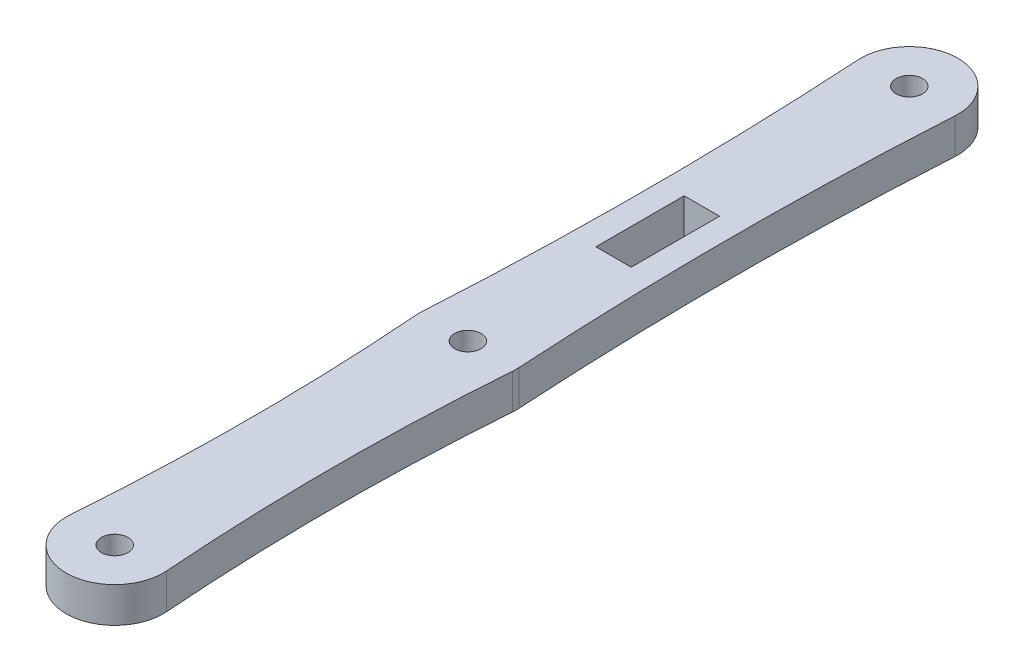
SolidWorks part; units mm, degrees
ref_plane "Front Plane" through (0, 0, 0) normal (0, 0, 1) x (1, 0, 0)
ref_plane "Top Plane" through (0, 0, 0) normal (0, 1, 0) x (1, 0, 0)
ref_plane "Right Plane" through (0, 0, 0) normal (1, 0, 0) x (0, 0, -1)
sketch "Sketch1" plane through (0, 0, 0) normal (0, 1, 0) x (1, 0, 0)
  line L0 (0, 0) -> (0, 90) construction
  line L3 (4.75, 65) -> (-4.75, 65) construction
  line L4 (4.75, 20) -> (-4.75, 20) construction
  line L6 (2, 56.5) -> (-2, 56.5)
  line L7 (2, 56.5) -> (2, 66.5)
  line L8 (2, 66.5) -> (-2, 66.5)
  line L9 (-2, 56.5) -> (-2, 66.5)
  circle A2 centre (0, 0) radius 1.5
  circle A3 centre (0, 90) radius 1.5
  arc A8 (-5.4846, 0.4119) -> (5.4846, 0.4119) centre (0, 0) ccw
  arc A9 (5.4901, 89.6703) -> (-5.4901, 89.6703) centre (0, 90) ccw
  circle A12 centre (0, 40) radius 1.5
  arc A13 (-5.4901, 40.3297) -> (-5.4846, 39.5881) centre (0, 40) ccw
  arc A14 (5.4846, 0.4119) -> (5.4846, 39.5881) centre (266.2917, 20) cw
  arc A15 (5.4901, 40.3297) -> (5.4901, 89.6703) centre (416.2917, 65) cw
  arc A16 (-5.4846, 0.4119) -> (-5.4846, 39.5881) centre (-266.2917, 20) ccw
  arc A17 (-5.4901, 40.3297) -> (-5.4901, 89.6703) centre (-416.2917, 65) ccw
  arc A18 (5.4846, 39.5881) -> (5.4901, 40.3297) centre (0, 40) ccw
  circle A19 centre (0, 65) radius 1.5 construction
  point P26 (0, 20)
  point P27 (0, 65)
  point P33 (-1.3122, 61.7212)
  point P34 (0, 66.5)
  dimension "D1" = 3
  dimension "D2" = 90
  dimension "D3" = 4
  dimension "D5" = 9.5
  dimension "D6" = 3
  dimension "D7" = 4
  dimension "D4" = 40
  dimension "D8" = 10
extrude "Boss-Extrude1" add sketch "Sketch1" along normal blind 4
